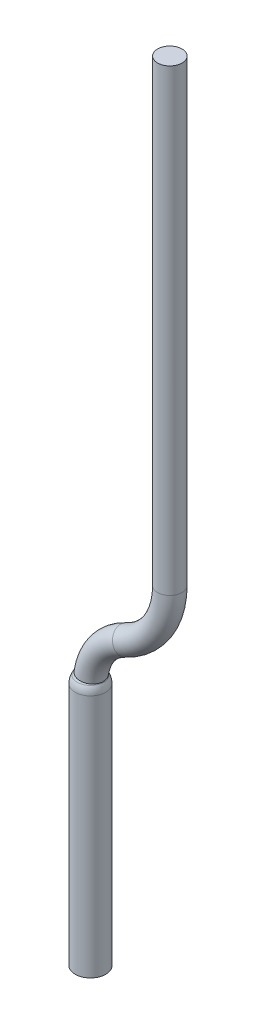
SolidWorks part; units mm, degrees
material "Copper"
ref_plane "Front Plane" through (0, 0, 0) normal (0, 0, 1) x (1, 0, 0)
ref_plane "Top Plane" through (0, 0, 0) normal (0, 1, 0) x (1, 0, 0)
ref_plane "Right Plane" through (0, 0, 0) normal (1, 0, 0) x (0, 0, -1)
sketch "Sketch1" plane through (0, 0, 0) normal (0, 0, 1) x (1, 0, 0)
  line L0 (-7.5, 54.2) -> (-7.5, 24.1584)
  line L2 (-12.7, 16) -> (-12.7, 0)
  line L3 (55, 0) -> (-55, 0) construction
  line L4 (0, -55) -> (0, 55) construction
  arc A0 (-12.7, 16) -> (-10.3889, 19.626) centre (-8.7, 16) cw
  arc A1 (-7.5, 24.1584) -> (-10.3889, 19.626) centre (-12.5, 24.1584) cw
  dimension "D1" = 4
  dimension "D6" = 5
  dimension "D2" = 12.7
  dimension "D3" = 5.2
  dimension "D4" = 16
  dimension "D5" = 54.2
sketch "Sketch2" plane through (0, 0, 0) normal (0, 1, 0) x (1, 0, 0)
  line L0 (-12.7, 0) -> (-10.3889, 0) construction
  line L1 (-55, 0) -> (55, 0) construction
  circle A0 centre (-12.7, 0) radius 0.8
  dimension "D1" = 1.6
sweep "Sweep1" add profiles "Sketch2" path "Sketch1"
sketch "Sketch3" plane through (0, 0, 0) normal (0, 0, 1) x (1, 0, 0)
  line L0 (-12.7, 21.8194) -> (-12.7, -3.5848) construction
  line L1 (0, -0.88) -> (0, 0.88) construction
  line L2 (-12.7, 0) -> (-11.7, 0)
  line L3 (0.88, 0) -> (-0.88, 0) construction
  line L4 (-11.7, 0) -> (-11.7, 16)
  line L5 (-11.834, 16.5) -> (-12.7, 18)
  line L6 (-12.7, 18) -> (-12.7, 0)
  arc A0 (-11.7, 16) -> (-11.834, 16.5) centre (-12.7, 16) ccw
  dimension "D2" = 1
  dimension "D1" = 12.7
  dimension "D3" = 2
  dimension "D4" = 16
  dimension "D5" = 30
revolve "Revolve1" add sketch "Sketch3" angle 360 about L0
